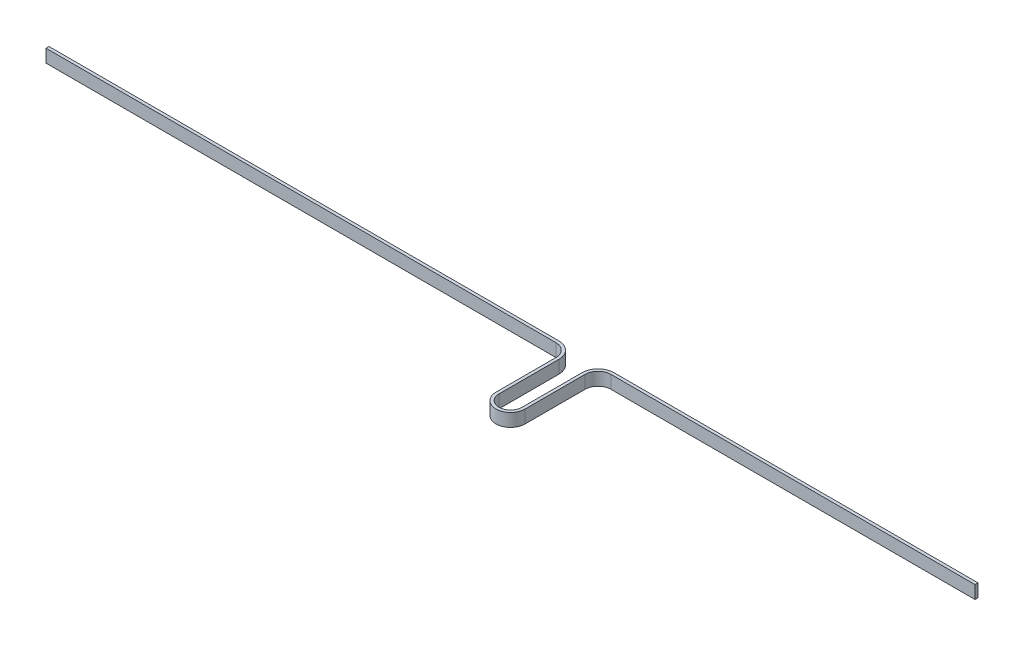
SolidWorks part; units mm, degrees
ref_plane "Front Plane" through (0, 0, 0) normal (0, 0, 1) x (1, 0, 0)
ref_plane "Top Plane" through (0, 0, 0) normal (0, 1, 0) x (1, 0, 0)
ref_plane "Right Plane" through (0, 0, 0) normal (1, 0, 0) x (0, 0, -1)
sketch "Sketch1" plane through (0, 0, 0) normal (0, 1, 0) x (1, 0, 0)
  line L1 (356.75, -267.0175) -> (356.75, -294.7675)
  line L2 (344.01, -294.7675) -> (344.01, -267.0175)
  line L3 (337.64, -260.6475) -> (101.625, -260.6475)
  line L6 (363.12, -260.6475) -> (531.6254, -260.6475)
  arc A0 (356.75, -294.7675) -> (344.01, -294.7675) centre (350.38, -294.7675) cw
  arc A1 (344.01, -267.0175) -> (337.64, -260.6475) centre (337.64, -267.0175) ccw
  arc A2 (363.12, -260.6475) -> (356.75, -267.0175) centre (363.12, -267.0175) ccw
  dimension "D1" = 6.37
  dimension "D2" = 6.37
  dimension "D5" = 168.5054
  dimension "D3" = 6.37
  dimension "D4" = 27.75
  dimension "D7" = 236.015
extrude "Extrude-Thin1" add sketch "Sketch1" along normal blind 6 thin thin type two direction wall 0.376 second wall 1.004
